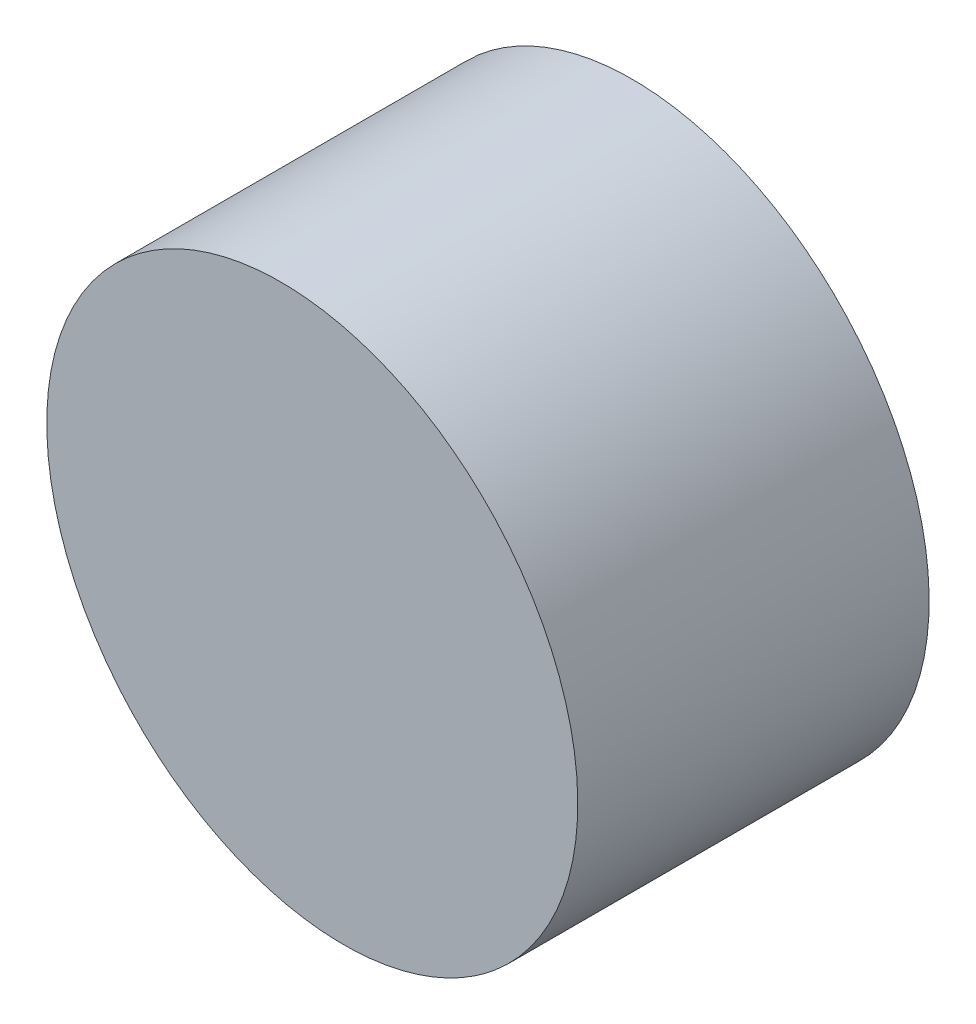
SolidWorks part; units mm, degrees
ref_plane "前视基准面" through (0, 0, 0) normal (0, 0, 1) x (1, 0, 0)
ref_plane "上视基准面" through (0, 0, 0) normal (0, 1, 0) x (1, 0, 0)
ref_plane "右视基准面" through (0, 0, 0) normal (1, 0, 0) x (0, 0, -1)
sketch "草图1" plane through (0, 0, 0) normal (0, 0, 1) x (1, 0, 0)
  ellipse E0 centre (0, 0) end of major axis (19.7354, -23.6554) minor radius 27.3034
extrude "凸台-拉伸1" add sketch "草图1" along normal blind 38.1 contours E0
